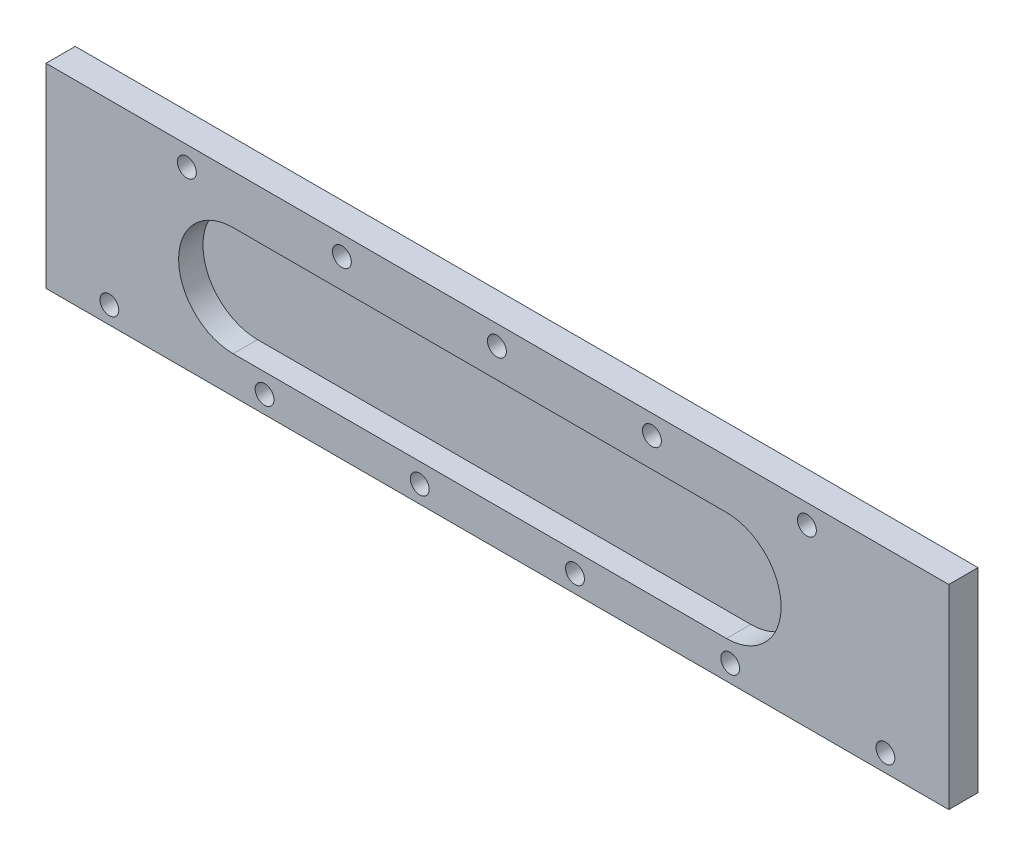
SolidWorks part; units mm, degrees
ref_plane "Front Plane" through (0, 0, 0) normal (0, 0, 1) x (1, 0, 0)
ref_plane "Top Plane" through (0, 0, 0) normal (0, 1, 0) x (1, 0, 0)
ref_plane "Right Plane" through (0, 0, 0) normal (1, 0, 0) x (0, 0, -1)
sketch "Sketch5" plane through (0, 0, 0) normal (0, 0, 1) x (1, 0, 0)
  line L1 (0, 0) -> (-235.204, 0)
  line L2 (0, 0) -> (0, 50.8)
  line L3 (0, 50.8) -> (-235.204, 50.8)
  line L4 (-235.204, 0) -> (-235.204, 50.8)
  dimension "D1" = 235.204
  dimension "D2" = 50.8
extrude "Boss-Extrude3" add sketch "Sketch5" along normal blind 7.62
sketch "Sketch6" plane through (0, 0, 7.62) normal (0, 0, 1) x (1, 0, 0)
  line L0 (0, 0) -> (0, 50.8) construction
  line L1 (0, 50.8) -> (-235.204, 50.8) construction
  line L3 (-57.912, 23.876) -> (-186.436, 23.876) construction
  line L7 (-57.912, 9.652) -> (-186.436, 9.652)
  line L8 (-57.912, 38.1) -> (-186.436, 38.1)
  arc A0 (-57.912, 9.652) -> (-57.912, 38.1) centre (-57.912, 23.876) ccw
  arc A1 (-186.436, 38.1) -> (-186.436, 9.652) centre (-186.436, 23.876) ccw
  point P14 (-122.174, 23.876)
  dimension "D4" = 57.912
  dimension "D2" = 128.524
  dimension "D1" = 28.448
  dimension "D3" = 26.924
extrude "Cut-Extrude3" cut sketch "Sketch6" against normal blind 6.35
sketch "Sketch7" plane through (0, 0, 7.62) normal (0, 0, 1) x (1, 0, 0)
  line L0 (-235.204, 50.8) -> (-235.204, 0) construction
  line L1 (0, 0) -> (0, 50.8) construction
  line L2 (0, 50.8) -> (-235.204, 50.8) construction
  circle A0 centre (-218.694, 4.5485) radius 1.7923
  circle A1 centre (-178.2572, 4.5485) radius 1.7923
  circle A2 centre (-137.8204, 4.5485) radius 1.7923
  circle A3 centre (-97.3836, 4.5485) radius 1.7923
  circle A4 centre (-56.9468, 4.5485) radius 1.7923
  circle A5 centre (-16.51, 4.5485) radius 1.7923
  circle A6 centre (-198.501, 45.72) radius 3.5223
  circle A7 centre (-158.115, 45.72) radius 3.5223
  circle A8 centre (-117.729, 45.72) radius 3.5223
  circle A9 centre (-77.343, 45.72) radius 3.5223
  circle A10 centre (-36.957, 45.72) radius 2.697
  dimension "D2" = 16.51
  dimension "D4" = 40.4368
  dimension "D6" = 20.193
  dimension "D8" = 40.386
  dimension "D3" = 16.51
  dimension "D7" = 40.386
  dimension "D9" = 5.08
  dimension "D10" = 5.08
  dimension "D1" = 6
  dimension "D5" = 4
hole_wizard "#10 (0.1935) Diameter Hole1" positions "3DSketch1" profile "Sketch8" hole size "#10" standard "ANSI Inch" end condition through all
sketch3d "3DSketch1"
  point P0 (-198.501, 45.72, 7.62)
  point P3 (-158.115, 45.72, 7.62)
  point P6 (-117.729, 45.72, 7.62)
  point P9 (-77.343, 45.72, 7.62)
  point P12 (-36.957, 45.72, 7.62)
  point P15 (-218.694, 4.5485, 7.62)
  point P18 (-178.2572, 4.5485, 7.62)
  point P21 (-137.8204, 4.5485, 7.62)
  point P24 (-97.3836, 4.5485, 7.62)
  point P27 (-56.9468, 4.5485, 7.62)
  point P30 (-16.51, 4.5485, 7.62)
sketch "Sketch8" plane through (-198.501, 45.72, 7.62) normal (1, 0, 0) x (0, -1, 0)
  line L0 (0, 0) -> (0, 7.62)
  line L1 (0, 7.62) -> (2.4574, 7.62)
  line L2 (2.4574, 7.62) -> (2.4574, 0)
  line L5 (2.4574, 0) -> (0, 0)
  line L11 (0, -6.35) -> (0, 107.95) construction
  dimension "Thru Hole Dia." = 4.9149
  dimension "Thru Hole Depth" = 7.62
